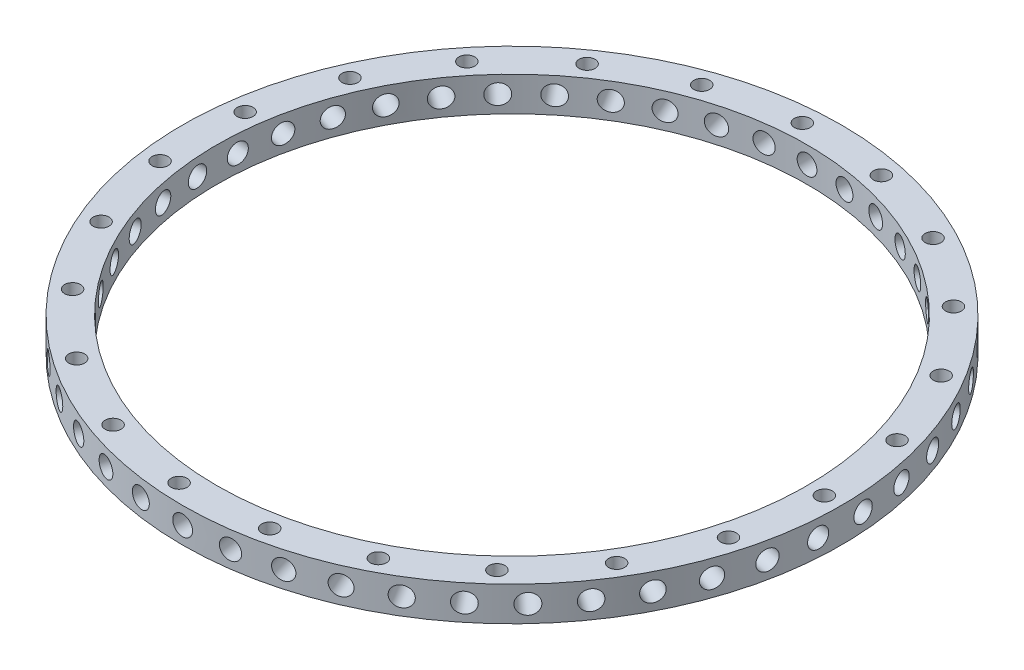
SolidWorks part; units mm, degrees
material "AISI 316 Stainless Steel Sheet (SS)"
ref_plane "Front Plane" through (0, 0, 0) normal (0, 0, 1) x (1, 0, 0)
ref_plane "Top Plane" through (0, 0, 0) normal (0, 1, 0) x (1, 0, 0)
ref_plane "Right Plane" through (0, 0, 0) normal (1, 0, 0) x (0, 0, -1)
sketch "Sketch1" plane through (0, 0, 0) normal (0, 1, 0) x (1, 0, 0)
  circle A0 centre (0, 0) radius 54.61
  circle A1 centre (0, 0) radius 60.96
  point P12 (0, 60.96)
  point P26 (0, 0)
  dimension "D1" = 121.92
  dimension "D2" = 6.35
extrude "Boss-Extrude1" add sketch "Sketch1" along normal blind 6.35 contours A1 A0
hole_wizard "#6 Clearance Hole2" positions "3DSketch2" profile "Sketch2" hole size "#6" standard "ANSI Inch"
sketch3d "3DSketch2"
  line L0 (0, 0, 60.96) -> (0, 6.35, 60.96) construction
  circle A4 centre (0, 6.35, 0) radius 60.96 construction
  circle A5 centre (0, 0, 0) radius 60.96 construction
  point P19 (0, 3.175, 60.96)
  point P23 (0, 3.175, 60.96)
  point P24 (0, 3.175, 60.96)
  point P26 (0, 3.175, 60.96)
  point P42 (0, 67.31, 0)
  point P46 (0, 60.96, 0)
sketch "Sketch2" plane through (0, 3.175, 60.96) normal (1, 0, 0) x (0, -1, 0)
  line L0 (0, 0) -> (0, 13.7989)
  line L1 (0, 13.7989) -> (1.8288, 12.7)
  line L2 (1.8288, 12.7) -> (1.8288, 0)
  line L5 (1.8288, 0) -> (0, 0)
  line L10 (0, 13.7989) -> (-1.8288, 12.7) construction
  line L11 (0, -6.35) -> (0, 107.95) construction
  dimension "Hole Dia." = 3.6576
  dimension "Hole Depth" = 12.7
  dimension "Drill Angle" = 118
pattern_circular "CirPattern1" count 46 over 360 about axis through (0, 6.35, 0) along (0, -1, 0) of "#6 Clearance Hole2"
hole_wizard "#4 Clearance Hole1" positions "3DSketch3" profile "Sketch3" hole size "#4" standard "ANSI Inch"
sketch3d "3DSketch3"
  line L1 (0, 6.35, 0) -> (0, 6.35, 60.96) construction
  line L4 (-4.1601, 6.35, 60.8179) -> (-3.7267, 6.35, 54.4827) construction
  circle A0 centre (0, 6.35, 0) radius 60.96 construction
  circle A1 centre (0, 6.35, 0) radius 54.61 construction
  point P0 (-3.9434, 6.35, 57.6503)
  point P9 (0, 67.31, 0)
  point P24 (0, 60.96, 0)
  point P26 (-3.9434, 6.35, 57.6503)
  dimension "D1" = 3.913
sketch "Sketch3" plane through (-3.9434, 6.35, 57.6503) normal (1, 0, 0) x (0, 0, 1)
  line L0 (0, 0) -> (0, 13.5852)
  line L1 (0, 13.5852) -> (1.4732, 12.7)
  line L2 (1.4732, 12.7) -> (1.4732, 0)
  line L5 (1.4732, 0) -> (0, 0)
  line L10 (0, 13.5852) -> (-1.4732, 12.7) construction
  line L11 (0, -6.35) -> (0, 107.95) construction
  dimension "Hole Dia." = 2.9464
  dimension "Hole Depth" = 12.7
  dimension "Drill Angle" = 118
pattern_circular "CirPattern2" count 23 over 360 about axis through (0, 0, 0) along (0, 1, 0) of "#4 Clearance Hole1"
equation "\"D1@CirPattern1\"=\"blade number@[TP] [Turb] Turbine.Assembly\""
equation "\"D1@Sketch1\"=2*\"rotor base@[TP] [Turb] Turbine.Assembly\""
equation "\"D1@CirPattern2\"=\"blade number@[TP] [Turb] Turbine.Assembly\"/2"
equation "\"D1@3DSketch3\"=360/\"blade number@[TP] [Turb] Turbine.Assembly\"/2"
